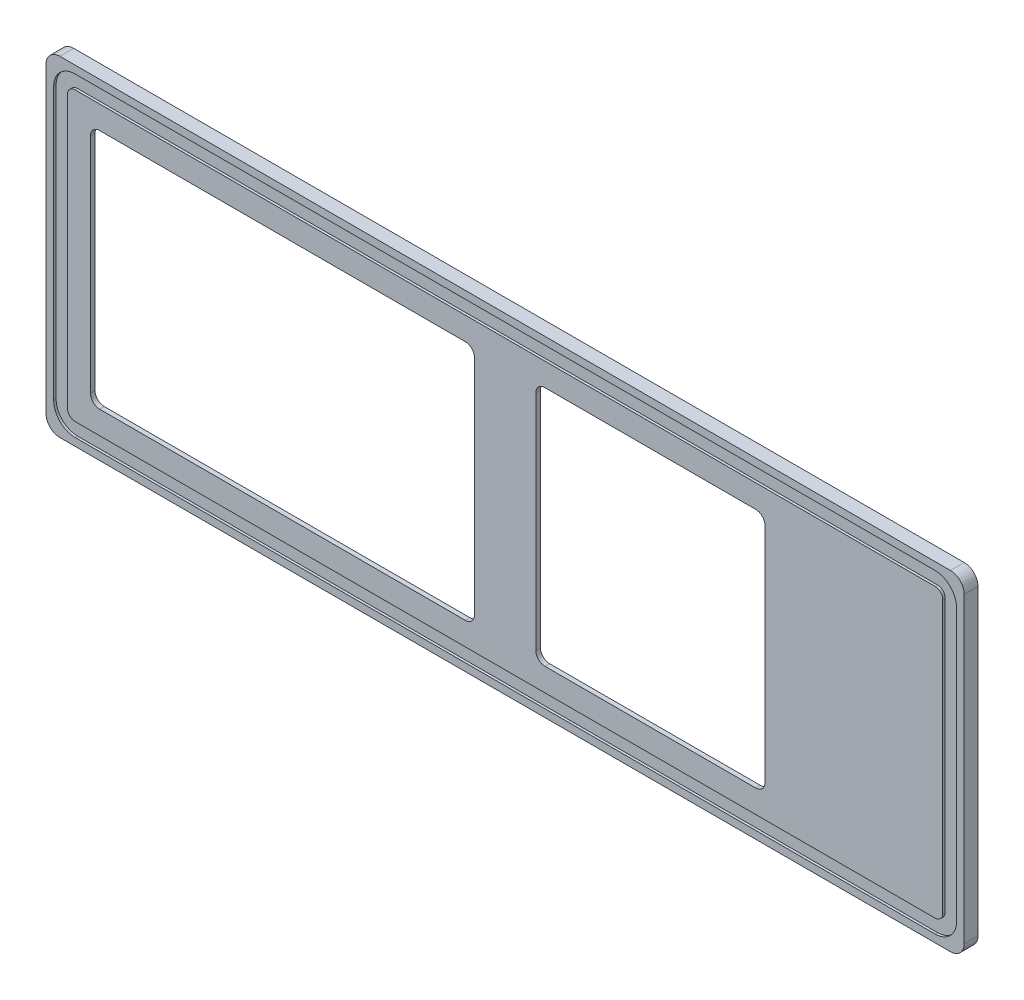
SolidWorks part; units mm, degrees
ref_plane "Front Plane" through (0, 0, 0) normal (0, 0, 1) x (1, 0, 0)
ref_plane "Top Plane" through (0, 0, 0) normal (0, 1, 0) x (1, 0, 0)
ref_plane "Right Plane" through (0, 0, 0) normal (1, 0, 0) x (0, 0, -1)
sketch "Sketch1" plane through (0, 0, 0) normal (0, 0, 1) x (1, 0, 0)
  line L11 (-290.5, 206.4) -> (290.5, 206.4)
  line L12 (299.5, 197.4) -> (299.5, 0)
  line L13 (290.5, -9) -> (-290.5, -9)
  line L14 (-299.5, 197.4) -> (-299.5, 0)
  arc A0 (-290.5, -9) -> (-299.5, 0) centre (-290.5, 0) cw
  arc A1 (290.5, -9) -> (299.5, 0) centre (290.5, 0) ccw
  arc A2 (290.5, 206.4) -> (299.5, 197.4) centre (290.5, 197.4) cw
  arc A3 (-290.5, 206.4) -> (-299.5, 197.4) centre (-290.5, 197.4) ccw
  point P12 (0, -9)
  dimension "D1" = 9
  dimension "D2" = 0
extrude "Boss-Extrude1" add sketch "Sketch1" along normal blind 9
sketch "Sketch4" plane through (0, 0, 9) normal (0, 0, 1) x (1, 0, 0)
  line L0 (290.5, 206.4) -> (-290.5, 206.4) construction
  line L1 (-299.5, 197.4) -> (-299.5, 0) construction
  line L2 (-290.5, -9) -> (290.5, -9) construction
  line L3 (299.5, 0) -> (299.5, 197.4) construction
  line L5 (-280.5, -4) -> (280.5, -4)
  line L6 (-294.5, 10) -> (-294.5, 187.4)
  line L7 (-280.5, 201.4) -> (280.5, 201.4)
  line L8 (294.5, 10) -> (294.5, 187.4)
  line L12 (-280.5, 5) -> (280.5, 5)
  line L13 (285.5, 10) -> (285.5, 187.4)
  line L14 (-280.5, 192.4) -> (280.5, 192.4)
  line L15 (-285.5, 10) -> (-285.5, 187.4)
  line L16 (-294.5, 201.4) -> (294.5, 201.4) construction
  line L17 (294.5, -4) -> (294.5, 201.4) construction
  line L18 (-294.5, -4) -> (294.5, -4) construction
  line L19 (-294.5, -4) -> (-294.5, 201.4) construction
  line L20 (285.5, 5) -> (285.5, 192.4) construction
  line L21 (-285.5, 192.4) -> (285.5, 192.4) construction
  line L22 (-285.5, 5) -> (285.5, 5) construction
  line L23 (-285.5, 5) -> (-285.5, 192.4) construction
  arc A4 (280.5, 201.4) -> (294.5, 187.4) centre (280.5, 187.4) cw
  arc A5 (280.5, -4) -> (294.5, 10) centre (280.5, 10) ccw
  arc A6 (-280.5, -4) -> (-294.5, 10) centre (-280.5, 10) cw
  arc A7 (-294.5, 187.4) -> (-280.5, 201.4) centre (-280.5, 187.4) cw
  arc A8 (285.5, 187.4) -> (280.5, 192.4) centre (280.5, 187.4) ccw
  arc A9 (280.5, 5) -> (285.5, 10) centre (280.5, 10) ccw
  arc A10 (-280.5, 5) -> (-285.5, 10) centre (-280.5, 10) cw
  arc A11 (-280.5, 192.4) -> (-285.5, 187.4) centre (-280.5, 187.4) ccw
  dimension "D6" = 14
  dimension "D7" = 5
  dimension "D1" = 5
  dimension "D2" = 5
  dimension "D3" = 5
  dimension "D4" = 5
  dimension "D5" = 9
extrude "Cut-Extrude1" cut sketch "Sketch4" against normal blind 1.6
sketch "Sketch5" plane through (0, 0, 0) normal (0, 0, 1) x (1, 0, 0)
  line L0 (-285.5, 187.4) -> (-285.5, 10) construction
  line L1 (-264.5, 177.4) -> (-26, 177.4)
  line L2 (-270.5, 171.4) -> (-270.5, 26)
  line L3 (-264.5, 20) -> (-26, 20)
  line L4 (-20, 171.4) -> (-20, 26)
  line L5 (280.5, 192.4) -> (-280.5, 192.4) construction
  line L6 (-280.5, 5) -> (280.5, 5) construction
  line L7 (-290.5, -9) -> (290.5, -9) construction
  line L8 (20, 171.4) -> (20, 26)
  line L9 (26, 20) -> (163.5, 20)
  line L10 (169.5, 26) -> (169.5, 171.4)
  line L11 (163.5, 177.4) -> (26, 177.4)
  line L12 (299.5, 0) -> (299.5, 197.4) construction
  arc A0 (-270.5, 26) -> (-264.5, 20) centre (-264.5, 26) ccw
  arc A1 (-26, 20) -> (-20, 26) centre (-26, 26) ccw
  arc A2 (-26, 177.4) -> (-20, 171.4) centre (-26, 171.4) cw
  arc A3 (-264.5, 177.4) -> (-270.5, 171.4) centre (-264.5, 171.4) ccw
  arc A4 (20, 171.4) -> (26, 177.4) centre (26, 171.4) cw
  arc A5 (20, 26) -> (26, 20) centre (26, 26) ccw
  arc A6 (163.5, 20) -> (169.5, 26) centre (163.5, 26) ccw
  arc A7 (169.5, 171.4) -> (163.5, 177.4) centre (163.5, 171.4) ccw
  point P20 (0, -9)
  dimension "D4" = 6
  dimension "D1" = 15
  dimension "D2" = 15
  dimension "D3" = 15
  dimension "D5" = 20
  dimension "D6" = 20
  dimension "D7" = 130
extrude "Cut-Extrude2" cut sketch "Sketch5" along normal up to surface (9 mm away) up to face at (0, 98.7, 9)
sketch "Sketch7" plane through (0, 0, 0) normal (0, 0, -1) x (-1, 0, 0)
  line L8 (280.5, 26) -> (280.5, 171.4)
  line L9 (26, 10) -> (264.5, 10)
  line L10 (10, 171.4) -> (10, 26)
  line L11 (264.5, 187.4) -> (26, 187.4)
  line L12 (280.5, 26) -> (280.5, 171.4)
  line L13 (26, 10) -> (264.5, 10)
  line L14 (10, 171.4) -> (10, 26)
  line L15 (264.5, 187.4) -> (26, 187.4)
  line L33 (-163.5, 10) -> (-26, 10)
  line L34 (-10, 26) -> (-10, 171.4)
  line L35 (-26, 187.4) -> (-163.5, 187.4)
  line L36 (-179.5, 171.4) -> (-179.5, 26)
  line L37 (-163.5, 10) -> (-26, 10)
  line L38 (-10, 26) -> (-10, 171.4)
  line L39 (-26, 187.4) -> (-163.5, 187.4)
  line L40 (-179.5, 171.4) -> (-179.5, 26)
  arc A8 (264.5, 10) -> (280.5, 26) centre (264.5, 26) ccw
  arc A9 (10, 26) -> (26, 10) centre (26, 26) ccw
  arc A10 (26, 187.4) -> (10, 171.4) centre (26, 171.4) ccw
  arc A11 (280.5, 171.4) -> (264.5, 187.4) centre (264.5, 171.4) ccw
  arc A12 (264.5, 10) -> (280.5, 26) centre (264.5, 26) ccw
  arc A13 (10, 26) -> (26, 10) centre (26, 26) ccw
  arc A14 (26, 187.4) -> (10, 171.4) centre (26, 171.4) ccw
  arc A15 (280.5, 171.4) -> (264.5, 187.4) centre (264.5, 171.4) ccw
  arc A27 (-179.5, 26) -> (-163.5, 10) centre (-163.5, 26) ccw
  arc A28 (-26, 10) -> (-10, 26) centre (-26, 26) ccw
  arc A29 (-10, 171.4) -> (-26, 187.4) centre (-26, 171.4) ccw
  arc A30 (-163.5, 187.4) -> (-179.5, 171.4) centre (-163.5, 171.4) ccw
  arc A31 (-179.5, 26) -> (-163.5, 10) centre (-163.5, 26) ccw
  arc A32 (-26, 10) -> (-10, 26) centre (-26, 26) ccw
  arc A33 (-10, 171.4) -> (-26, 187.4) centre (-26, 171.4) ccw
  arc A34 (-163.5, 187.4) -> (-179.5, 171.4) centre (-163.5, 171.4) ccw
  dimension "D1" = 10
  dimension "D2" = 10
extrude "Cut-Extrude4" cut sketch "Sketch7" against normal blind 6
